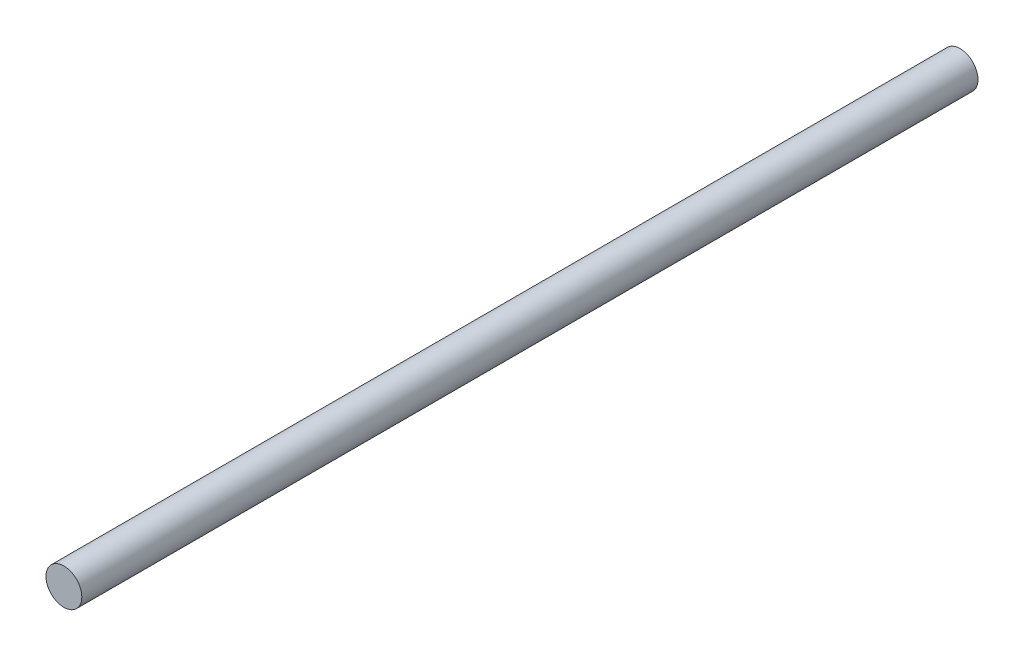
SolidWorks part; units mm, degrees
ref_plane "Front Plane" through (0, 0, 0) normal (0, 0, 1) x (1, 0, 0)
ref_plane "Top Plane" through (0, 0, 0) normal (0, 1, 0) x (1, 0, 0)
ref_plane "Right Plane" through (0, 0, 0) normal (1, 0, 0) x (0, 0, -1)
sketch "Sketch1" plane through (0, 0, 0) normal (0, 0, 1) x (1, 0, 0)
  circle A0 centre (0, 0) radius 4
  dimension "D1" = 8
extrude "Boss-Extrude1" add sketch "Sketch1" along normal blind 200
